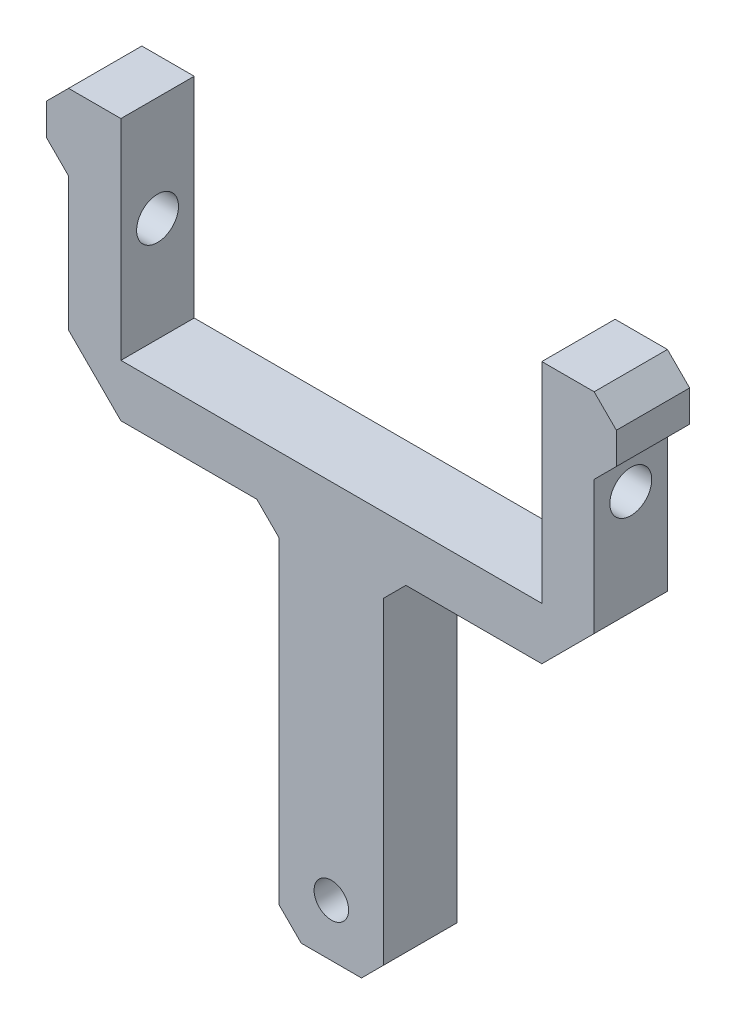
SolidWorks part; units mm, degrees
ref_plane "Alzado" through (0, 0, 0) normal (0, 0, 1) x (1, 0, 0)
ref_plane "Planta" through (0, 0, 0) normal (0, 1, 0) x (1, 0, 0)
ref_plane "Vista lateral" through (0, 0, 0) normal (1, 0, 0) x (0, 0, -1)
sketch "Croquis1" plane through (0, 0, 0) normal (0, 0, 1) x (1, 0, 0)
  line L0 (0, 0) -> (0, 44.6) construction
  line L1 (-5, 5) -> (5, 5)
  line L2 (-5, 5) -> (-5, -5)
  line L3 (-5, -5) -> (5, -5)
  line L4 (5, 5) -> (5, -5)
  line L5 (-5, 5) -> (5, -5) construction
  line L6 (-5, -5) -> (5, 5) construction
  line L7 (-20.1, 54.6) -> (-25.1, 54.6)
  line L8 (-20.1, 54.6) -> (20.1, 54.6)
  line L9 (-20.1, 54.6) -> (-20.1, 34.6)
  line L10 (-20.1, 34.6) -> (20.1, 34.6)
  line L12 (-20.1, 54.6) -> (20.1, 34.6) construction
  line L13 (-20.1, 34.6) -> (20.1, 54.6) construction
  line L18 (-25.1, 54.6) -> (-27.2213, 52.4787)
  line L19 (-27.2213, 52.4787) -> (-27.2213, 49.4787)
  line L20 (-27.2213, 49.4787) -> (-25.1, 47.3574)
  line L21 (-25.1, 47.3574) -> (-25.1, 34.5974)
  line L22 (20.1, 54.6) -> (20.1, 34.6)
  line L23 (-25.1, 34.5974) -> (-20.1026, 29.6)
  line L24 (-7.1213, 29.6) -> (-20.1026, 29.6)
  line L25 (-5, 27.4787) -> (-7.1213, 29.6)
  line L26 (-5, 5) -> (-5, 27.4787)
  line L27 (25.1, 47.3574) -> (25.1, 34.5974)
  line L28 (27.2213, 49.4787) -> (25.1, 47.3574)
  line L29 (25.1, 54.6) -> (27.2213, 52.4787)
  line L30 (27.2213, 52.4787) -> (27.2213, 49.4787)
  line L31 (20.1, 54.6) -> (25.1, 54.6)
  line L32 (25.1, 34.5974) -> (20.1026, 29.6)
  line L33 (7.1213, 29.6) -> (20.1026, 29.6)
  line L34 (5, 27.4787) -> (7.1213, 29.6)
  line L35 (5, 5) -> (5, 27.4787)
  circle A0 centre (0, 0) radius 1.65
  point P0 (0, 0)
  point P29 (-13.612, 29.6)
  dimension "D2" = 3.3
  dimension "D1" = 10
  dimension "D3" = 40.2
  dimension "D4" = 20
  dimension "D5" = 5
  dimension "D6" = 44.6
  dimension "D7" = 3
  dimension "D8" = 3
  dimension "D9" = 3
  dimension "D10" = 12.76
  dimension "D11" = 135
  dimension "D12" = 3
  dimension "D13" = 5
  dimension "D14" = 135
  dimension "D15" = 10
extrude "Saliente-Extruir1" add sketch "Croquis1" along normal blind 7
sketch "Croquis2" plane through (0, 0, 0) normal (0, 0, -1) x (-1, 0, 0)
  line L0 (-5, -5) -> (-2.8787, -5)
  line L1 (5, -5) -> (-5, -5) construction
  line L2 (-2.8787, -5) -> (-5, -2.8787)
  line L3 (-5, -5) -> (-5, 27.4787) construction
  line L4 (-5, -2.8787) -> (-5, -5)
  line L5 (0, 55) -> (0, -55) construction
  line L6 (2.8787, -5) -> (5, -2.8787)
  line L7 (5, -5) -> (2.8787, -5)
  line L8 (5, -2.8787) -> (5, -5)
  dimension "D1" = 45
  dimension "D2" = 3
extrude "Cortar-Extruir1" cut sketch "Croquis2" against normal through all
sketch "Croquis3" plane through (-25.1, 0, 0) normal (-1, 0, 0) x (0, 0, 1)
  line L0 (3.5, 34.5974) -> (3.5, 44.5974) construction
  line L1 (7, 34.5974) -> (0, 34.5974) construction
  circle A0 centre (3.5, 44.5974) radius 2
  dimension "D1" = 4
extrude "Cortar-Extruir3" cut sketch "Croquis3" against normal through all
sketch "Croquis4" plane through (-25.1, 0, 0) normal (-1, 0, 0) x (0, 0, 1)
  circle A0 centre (3.5, 44.5974) radius 3.75
  dimension "D1" = 7.5
extrude "Cortar-Extruir4" cut sketch "Croquis4" along normal through all
sketch "Croquis5" plane through (25.1, 0, 0) normal (1, 0, 0) x (0, 0, -1)
  circle A0 centre (-3.5, 44.5974) radius 3.75
extrude "Cortar-Extruir5" cut sketch "Croquis5" along normal through all
